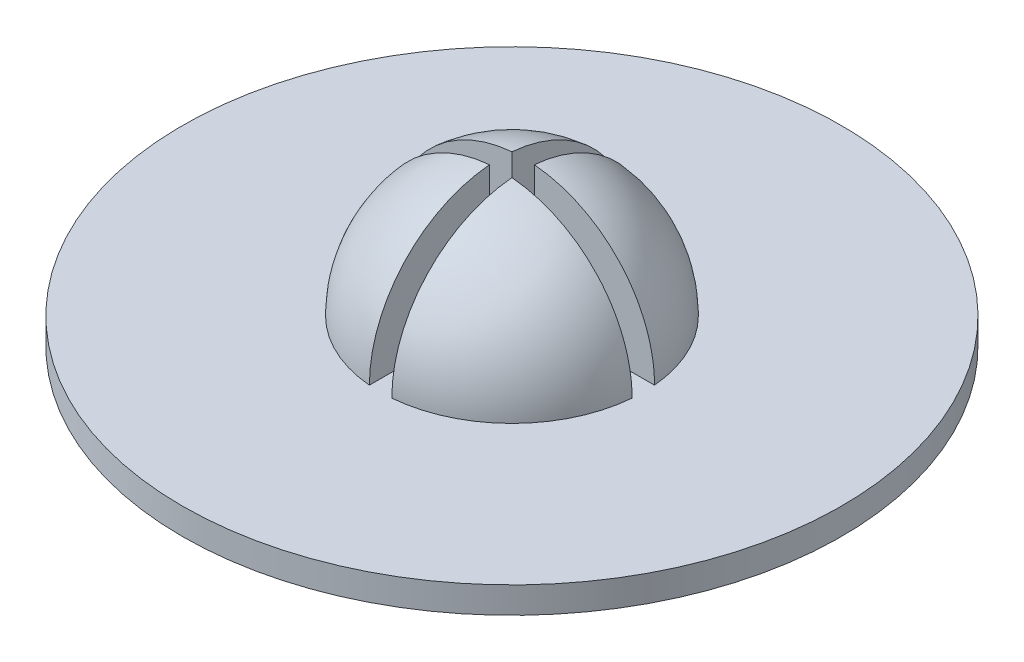
SolidWorks part; units mm, degrees
ref_plane "Front Plane" through (0, 0, 0) normal (0, 0, 1) x (1, 0, 0)
ref_plane "Top Plane" through (0, 0, 0) normal (0, 1, 0) x (1, 0, 0)
ref_plane "Right Plane" through (0, 0, 0) normal (1, 0, 0) x (0, 0, -1)
sketch "Sketch1" plane through (0, 0, 0) normal (0, 1, 0) x (1, 0, 0)
  circle A0 centre (0, 0) radius 25
  point P3 (0, 0)
  dimension "D1" = 50
extrude "Boss-Extrude1" add sketch "Sketch1" against normal blind 2
sketch "Sketch6" plane through (0, 0, 0) normal (0, 1, 0) x (1, 0, 0)
  line L0 (-10, 0) -> (10, 0)
  arc A0 (10, 0) -> (-10, 0) centre (0, 0) ccw
  point P4 (0, 0)
  point P5 (0, 0)
  dimension "D1" = 20
revolve "Revolve3" add sketch "Sketch6" angle 180 about L0
sketch "Sketch7" plane through (0, 0, 0) normal (0, 1, 0) x (1, 0, 0)
  line L0 (0, 0) -> (10, 0) construction
  line L1 (10, 0) -> (10, -0.85) construction
  line L2 (0, 10) -> (0, -10) construction
  line L3 (0, 10) -> (-0.85, 10) construction
  line L4 (0, 0) -> (-10, 0) construction
  line L5 (-10, 0) -> (-10, 0.85) construction
  line L6 (0, -10) -> (0.85, -10) construction
  line L8 (-0.85, 10) -> (0.85, 10)
  line L9 (-0.85, 10) -> (-0.85, -10)
  line L10 (-0.85, -10) -> (0.85, -10)
  line L11 (0.85, 10) -> (0.85, -10)
  line L12 (-10, 0.85) -> (10, 0.85)
  line L13 (-10, 0.85) -> (-10, -0.85)
  line L14 (-10, -0.85) -> (10, -0.85)
  line L15 (10, 0.85) -> (10, -0.85)
  circle A0 centre (0, 0) radius 10 construction
  dimension "D1" = 1.7
  dimension "D2" = 1.7
  dimension "D3" = 20
  dimension "D4" = 20
extrude "Cut-Extrude1" cut sketch "Sketch7" along normal blind 10 contours L9 L14 L11 L12 | L13 L14 L9 L12 | L9 L12 L11 L8 | L15 L12 L11 L14 | L14 L9 L10 L11
